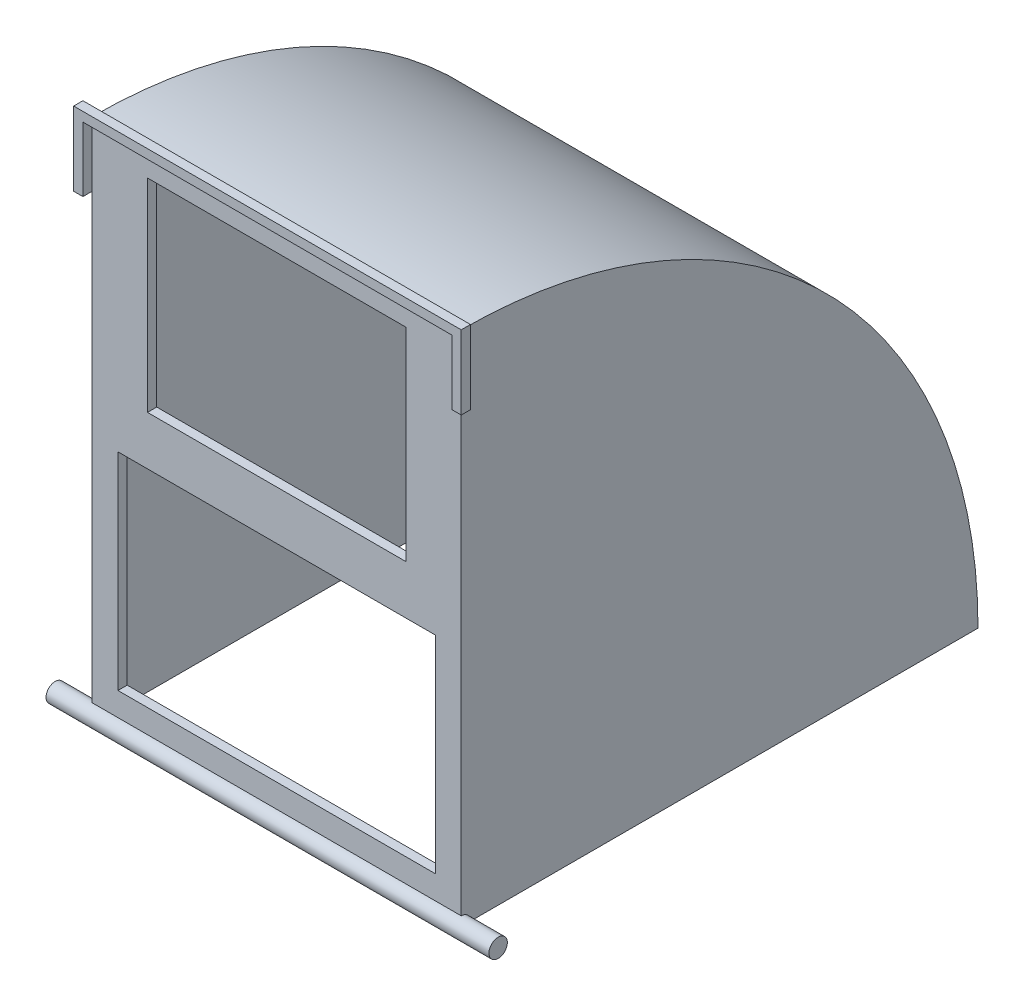
SolidWorks part; units mm, degrees
ref_plane "Front Plane" through (0, 0, 0) normal (0, 0, 1) x (1, 0, 0)
ref_plane "Top Plane" through (0, 0, 0) normal (0, 1, 0) x (1, 0, 0)
ref_plane "Right Plane" through (0, 0, 0) normal (1, 0, 0) x (0, 0, -1)
sketch "Sketch1" plane through (0, 0, 0) normal (1, 0, 0) x (0, 0, -1)
  line L0 (0, 0) -> (0, 177.8)
  line L1 (0, 0) -> (177.8, 0)
  arc A0 (177.8, 0) -> (0, 177.8) centre (0, 0) ccw
  dimension "D1" = 355.6
extrude "Boss-Extrude1" add sketch "Sketch1" along normal blind 127
sketch "Sketch2" plane through (0, 0, 0) normal (0, 0, 1) x (1, 0, 0)
  line L0 (0, 155.575) -> (-3.175, 155.575)
  line L1 (127, 155.575) -> (130.175, 155.575)
  line L2 (127, 155.575) -> (127, 177.8)
  line L3 (127, 177.8) -> (0, 177.8)
  line L4 (0, 155.575) -> (0, 177.8)
  line L12 (130.175, 180.975) -> (130.175, 155.575)
  line L13 (-3.175, 180.975) -> (130.175, 180.975)
  line L14 (-3.175, 155.575) -> (-3.175, 180.975)
  dimension "D2" = 25.4
  dimension "D1" = 25.4
extrude "Boss-Extrude2" add sketch "Sketch2" along normal blind 3.175 separate body
sketch "Sketch4" plane through (127, 0, 0) normal (1, 0, 0) x (0, 0, -1)
  circle A0 centre (0, 0) radius 3.175
  dimension "D1" = 6.35
extrude "Boss-Extrude7" add sketch "Sketch4" along normal blind 12.7 and the other way blind 139.7
sketch "Sketch5" plane through (0, 0, 0) normal (0, 0, 1) x (1, 0, 0)
  line L0 (0, 90.4875) -> (127, 90.4875) construction
  line L1 (0, 177.8) -> (0, 3.175) construction
  line L2 (127, 177.8) -> (127, 3.175) construction
  line L3 (63.5, 177.8) -> (63.5, 90.4875) construction
  line L4 (127, 177.8) -> (0, 177.8) construction
  line L6 (63.5, 134.1438) -> (0, 134.1438) construction
  line L7 (0, 134.1438) -> (127, 134.1438) construction
  line L8 (63.5, 90.4875) -> (63.5, 3.175) construction
  line L9 (107.95, 169.0687) -> (19.05, 169.0687)
  line L10 (107.95, 169.0687) -> (107.95, 99.2187)
  line L11 (107.95, 99.2187) -> (19.05, 99.2187)
  line L12 (19.05, 169.0687) -> (19.05, 99.2187)
  line L13 (107.95, 169.0687) -> (19.05, 99.2187) construction
  line L14 (107.95, 99.2187) -> (19.05, 169.0687) construction
  line L15 (0, 3.175) -> (127, 3.175) construction
  line L16 (63.5, 3.175) -> (63.5, 46.8312) construction
  line L17 (63.5, 46.8312) -> (0, 46.8312) construction
  line L18 (0, 46.8312) -> (127, 46.8312) construction
  line L20 (118.11, 82.3912) -> (8.89, 82.3912)
  line L21 (118.11, 82.3912) -> (118.11, 11.2713)
  line L22 (118.11, 11.2713) -> (8.89, 11.2712)
  line L23 (8.89, 82.3912) -> (8.89, 11.2712)
  line L24 (118.11, 82.3912) -> (8.89, 11.2712) construction
  line L25 (118.11, 11.2713) -> (8.89, 82.3912) construction
  dimension "D1" = 69.85
  dimension "D2" = 88.9
  dimension "D3" = 71.12
  dimension "D4" = 109.22
extrude "Cut-Extrude2" cut sketch "Sketch5" against normal blind 5.08
sketch "Sketch6" plane through (0, 0, 0) normal (-1, 0, 0) x (0, 0, 1)
  line L5 (-3.175, 3.175) -> (-174.5961, 3.175)
  line L6 (-3.175, 174.5961) -> (-3.175, 3.175)
  line L7 (-3.175, 3.175) -> (-174.5961, 3.175)
  line L8 (-3.175, 174.5961) -> (-3.175, 3.175)
  arc A4 (-3.175, 174.5961) -> (-174.5961, 3.175) centre (0, 0) ccw
  arc A5 (-3.175, 174.5961) -> (-174.5961, 3.175) centre (0, 0) ccw
  dimension "D1" = 3.175
extrude "Cut-Extrude3" cut sketch "Sketch6" against normal up to next (127 mm away)
sketch "Sketch7" plane through (0, 0, 0) normal (0, -1, 0) x (1, 0, 0)
  line L8 (123.825, -174.625) -> (123.825, -6.35)
  line L9 (123.825, -6.35) -> (3.175, -6.35)
  line L10 (3.175, -6.35) -> (3.175, -174.625)
  line L11 (3.175, -174.625) -> (123.825, -174.625)
  line L12 (123.825, -174.625) -> (123.825, -6.35)
  line L13 (123.825, -6.35) -> (3.175, -6.35)
  line L14 (3.175, -6.35) -> (3.175, -174.625)
  line L15 (3.175, -174.625) -> (123.825, -174.625)
  dimension "D1" = 3.175
extrude "Cut-Extrude4" cut sketch "Sketch7" against normal up to surface (3.175 mm away) up to face at (63.5, 3.175, -88.8856)
sketch "Sketch8" plane through (0, 0, 0) normal (-1, 0, 0) x (0, 0, 1)
  line L7 (-176.5254, 1.27) -> (-4.2597, 1.27)
  line L8 (-1.27, 4.2597) -> (-1.27, 176.5254)
  line L9 (-176.5254, 1.27) -> (-4.2597, 1.27)
  line L10 (-1.27, 4.2597) -> (-1.27, 176.5254)
  arc A7 (-1.27, 4.2597) -> (-4.2597, 1.27) centre (0, 0) ccw
  arc A8 (-1.27, 176.5254) -> (-176.5254, 1.27) centre (0, 0) ccw
  arc A9 (-1.27, 4.2597) -> (-4.2597, 1.27) centre (0, 0) ccw
  arc A10 (-1.27, 176.5254) -> (-176.5254, 1.27) centre (0, 0) ccw
  dimension "D1" = 1.27
extrude "Boss-Extrude9" add sketch "Sketch8" against normal blind 3.175
sketch "Sketch9" plane through (127, 0, 0) normal (1, 0, 0) x (0, 0, -1)
  line L4 (4.2597, 1.27) -> (176.5254, 1.27)
  line L5 (1.27, 176.5254) -> (1.27, 4.2597)
  line L6 (4.2597, 1.27) -> (176.5254, 1.27)
  line L7 (1.27, 176.5254) -> (1.27, 4.2597)
  arc A4 (4.2597, 1.27) -> (1.27, 4.2597) centre (0, 0) ccw
  arc A5 (176.5254, 1.27) -> (1.27, 176.5254) centre (0, 0) ccw
  arc A6 (4.2597, 1.27) -> (1.27, 4.2597) centre (0, 0) ccw
  arc A7 (176.5254, 1.27) -> (1.27, 176.5254) centre (0, 0) ccw
  dimension "D1" = 1.27
extrude "Boss-Extrude10" add sketch "Sketch9" against normal blind 3.175
